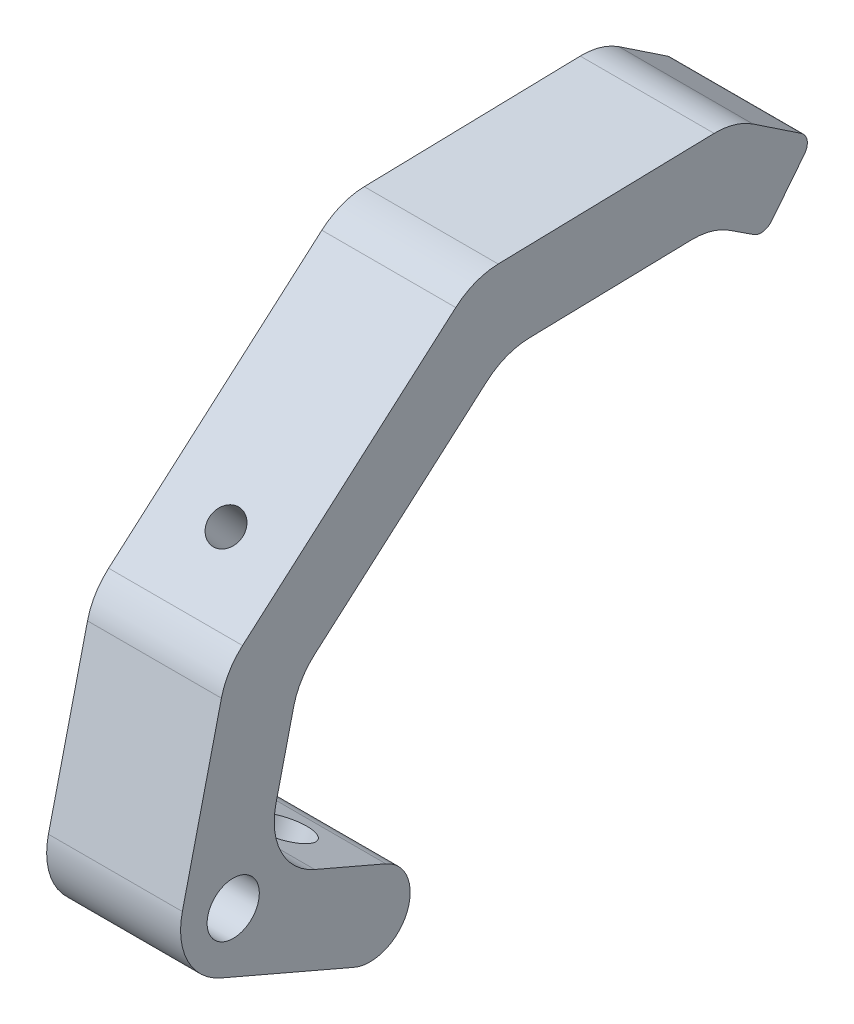
SolidWorks part; units mm, degrees
material "ABS"
ref_plane "Front Plane" through (0, 0, 0) normal (0, 0, 1) x (1, 0, 0)
ref_plane "Top Plane" through (0, 0, 0) normal (0, 1, 0) x (1, 0, 0)
ref_plane "Right Plane" through (0, 0, 0) normal (1, 0, 0) x (0, 0, -1)
sketch "Sketch1" plane through (0, 0, 0) normal (1, 0, 0) x (0, 0, -1)
  line L0 (0, 0) -> (8.7649, 37.0781) construction
  line L1 (8.7649, 37.0781) -> (51.818, 74.6621) construction
  line L2 (51.818, 74.6621) -> (96.268, 75.7173) construction
  line L3 (0, 0) -> (29.1607, -12.5586) construction
  line L13 (8.7649, 37.0781) -> (1.9118, 41.2106) construction
  line L18 (96.268, 75.7173) -> (108.0658, 68.0195) construction
  line L19 (103.9019, 61.6378) -> (113.2797, 73.4836)
  line L20 (98.4514, 83.3913) -> (113.2797, 73.4836)
  line L23 (48.8825, 82.2146) -> (98.4514, 83.3913)
  line L24 (1.9118, 41.2106) -> (48.8825, 82.2146)
  line L25 (-8.8866, -4.4695) -> (1.9118, 41.2106)
  line L26 (-8.8866, -4.4695) -> (26.1466, -19.5572)
  line L27 (94.0846, 68.0433) -> (103.9019, 61.6378)
  line L28 (54.7535, 67.1096) -> (94.0846, 68.0433)
  line L29 (15.6181, 32.9457) -> (54.7535, 67.1096)
  line L30 (8.8866, 4.4695) -> (15.6181, 32.9457)
  line L31 (8.8866, 4.4695) -> (32.1747, -5.56)
  line L32 (-8.8866, -4.4695) -> (8.8866, 4.4695) construction
  line L35 (98.4514, 83.3913) -> (112.2297, 74.4012) construction
  arc A3 (26.1466, -19.5572) -> (32.1747, -5.56) centre (29.1607, -12.5586) ccw
  circle A5 centre (3.2136, 1.6163) radius 4.953
  dimension "D10" = 9.906
  dimension "D11" = 7.62
  dimension "D9" = 145.516
  dimension "D16" = 6.35
  dimension "D2" = 31.75
  dimension "D3" = 38.1
  dimension "D4" = 57.15
  dimension "D5" = 44.45
  dimension "D6" = 100
  dimension "D7" = 144.42
  dimension "D12" = 60.7677
  dimension "D13" = 112.7779
  dimension "D8" = 140.24
  dimension "D14" = 15.1085
  dimension "D15" = 17.8337
  dimension "D17" = 19.8944
extrude "Boss-Extrude1" add sketch "Sketch1" along normal blind 25.4
fillet "Fillet1" radius 12.7 8 edges at (12.7, 67.1096, -54.7535) (12.7, 32.9457, -15.6181) (12.7, 4.4695, -8.8866) (12.7, 82.2146, -48.8825) (12.7, 41.2106, -1.9118) (12.7, -4.4695, 8.8866) (12.7, 68.0433, -94.0846) (12.7, 83.3913, -98.4514)
fillet "Fillet2" radius 2.54 2 edges at (12.7, 73.4836, -113.2797) (12.7, 61.6378, -103.9019)
sketch "Sketch5" plane through (0, -6.9986, 3.0141) normal (0, -0.9184, 0.3955) x (1, 0, 0)
  line L0 (25.4, -31.75) -> (0, -31.75) construction
  line L1 (12.7, -31.75) -> (12.7, -25.7249) construction
  circle A0 centre (12.7, -24.13) radius 5.08
  dimension "D1" = 10.16
  dimension "D2" = 7.62
extrude "Cut-Extrude3" cut sketch "Sketch5" against normal up to next
sketch "Sketch7" plane through (0, 22.4404, 19.5898) normal (0, 0.7533, 0.6576) x (1, 0, 0)
  line L0 (0, 32.6169) -> (25.4, 32.6169) construction
  line L1 (12.7, 32.6169) -> (12.7, 86.2999) construction
  line L2 (25.4, 86.2999) -> (0, 86.2999) construction
  circle A0 centre (12.7, 45.3169) radius 3.175
  point P8 (0, 0)
  dimension "D1" = 12.7
  dimension "D2" = 6.35
extrude "Cut-Extrude4" cut sketch "Sketch7" against normal up to next
